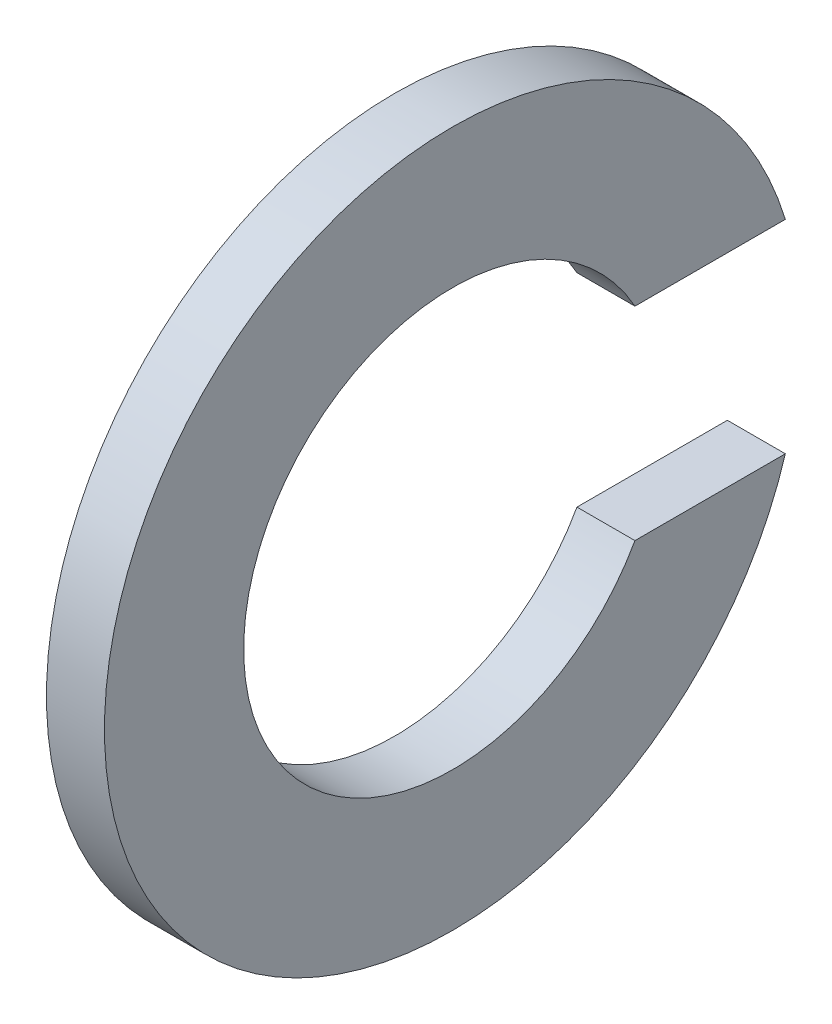
SolidWorks part; units mm, degrees
ref_plane "Front Plane" through (0, 0, 0) normal (0, 0, 1) x (1, 0, 0)
ref_plane "Top Plane" through (0, 0, 0) normal (0, 1, 0) x (1, 0, 0)
ref_plane "Right Plane" through (0, 0, 0) normal (1, 0, 0) x (0, 0, -1)
sketch "Sketch1" plane through (0, 0, 0) normal (1, 0, 0) x (0, 0, -1)
  line L0 (3.146, 1.75) -> (5.7391, 1.75)
  line L1 (3.146, -1.75) -> (5.7391, -1.75)
  line L2 (0, 0) -> (5, 0) construction
  arc A0 (5.7391, 1.75) -> (5.7391, -1.75) centre (0, 0) ccw
  arc A1 (3.146, 1.75) -> (3.146, -1.75) centre (0, 0) ccw
  dimension "D1" = 7.2
  dimension "D2" = 12
  dimension "D3" = 3.5
extrude "Boss-Extrude1" add sketch "Sketch1" along normal mid plane 1
